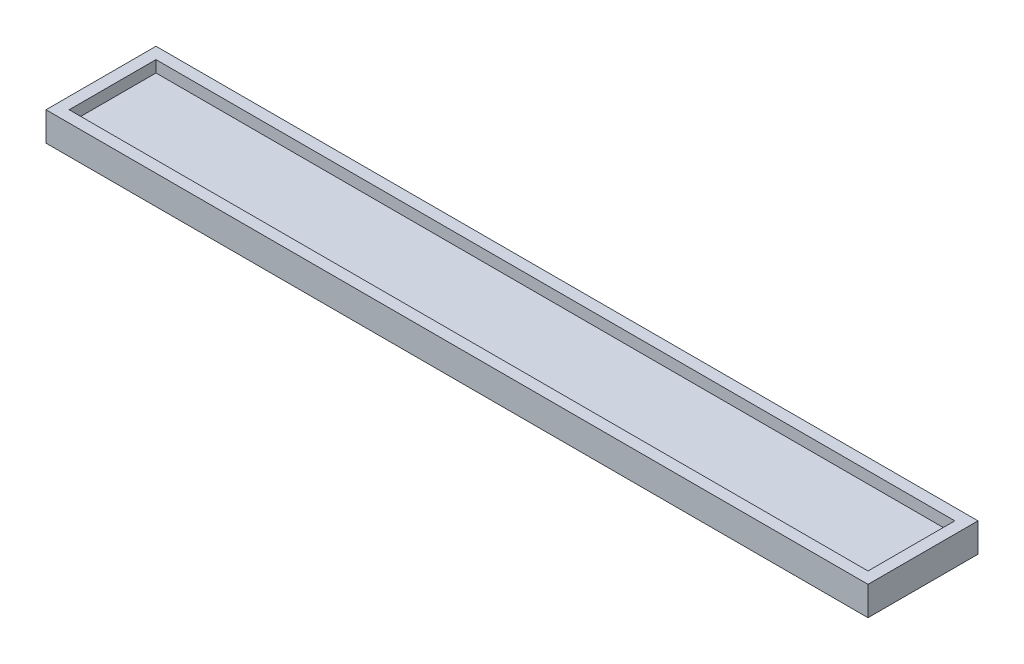
SolidWorks part; units mm, degrees
ref_plane "Front Plane" through (0, 0, 0) normal (0, 0, 1) x (1, 0, 0)
ref_plane "Top Plane" through (0, 0, 0) normal (0, 1, 0) x (1, 0, 0)
ref_plane "Right Plane" through (0, 0, 0) normal (1, 0, 0) x (0, 0, -1)
sketch "Sketch1" plane through (0, 0, 0) normal (0, 1, 0) x (1, 0, 0)
  line L1 (0, 0) -> (138, 0)
  line L2 (0, 0) -> (0, 15)
  line L3 (0, 15) -> (138, 15)
  line L4 (138, 0) -> (138, 15)
  dimension "D1" = 138
  dimension "D2" = 15
extrude "Boss-Extrude1" add sketch "Sketch1" along normal blind 3
sketch "Sketch2" plane through (0, 0, 0) normal (0, -1, 0) x (1, 0, 0)
  line L0 (-2, 2) -> (-2, -17)
  line L1 (0, 0) -> (138, 0)
  line L2 (0, 0) -> (0, -15)
  line L3 (0, -15) -> (138, -15)
  line L4 (138, 0) -> (138, -15)
  line L5 (-2, -17) -> (140, -17)
  line L6 (140, 2) -> (140, -17)
  line L7 (-2, 2) -> (140, 2)
  dimension "D1" = 2
extrude "Boss-Extrude2" add sketch "Sketch2" against normal offset from surface (5 mm away) 2 up to face at (69, 3, -7.5) offset beyond the face yes
